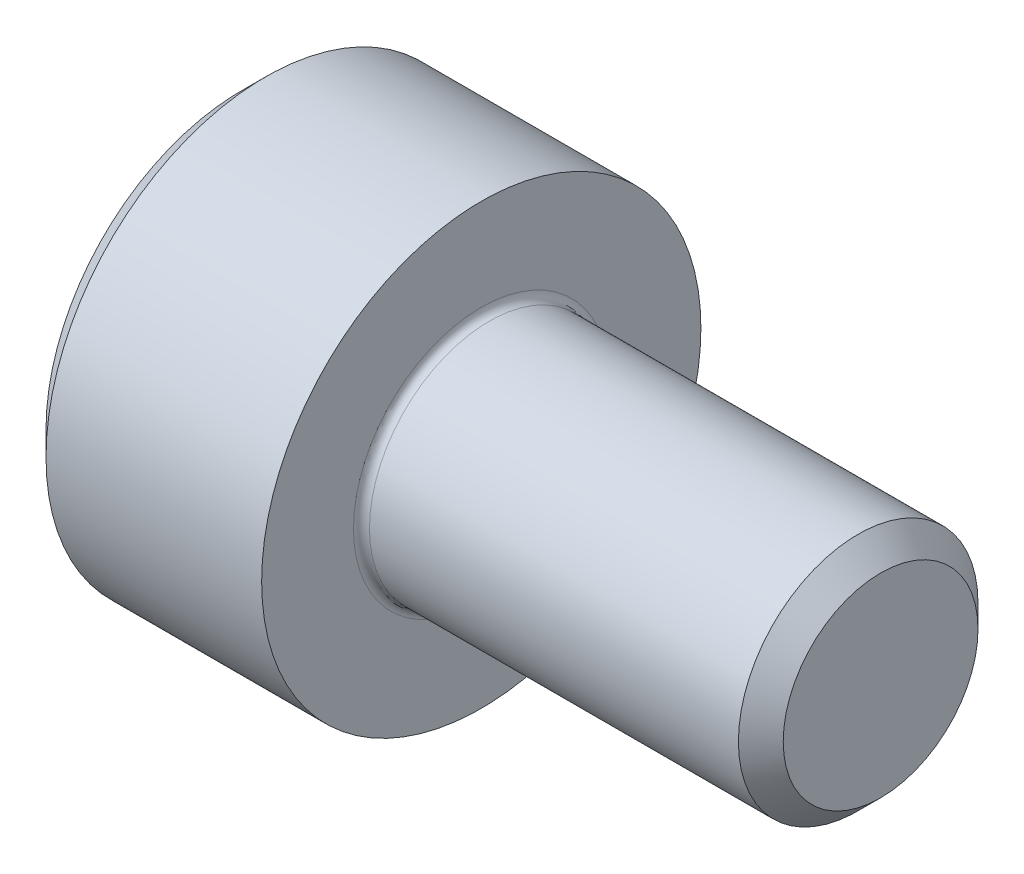
SolidWorks part; units mm, degrees
revolve "Base-Revolve" add sketch "BodySke"
sketch "BodySke" plane through (0, 0, 0) normal (0, 0, 1) x (1, 0, 0)
  line L0 (0, 0) -> (0, 2.45)
  line L1 (0.3, 2.75) -> (3, 2.75)
  line L2 (3, 2.75) -> (3, 1.5)
  line L3 (3, 1.5) -> (7.7195, 1.5)
  line L4 (8, 1.2195) -> (8, 0)
  line L5 (8, 0) -> (0, 0)
  line L6 (-31.75, 0) -> (127, 0) construction
  line L7 (0, 2.45) -> (0.3, 2.75)
  line L8 (8, 1.2195) -> (7.7195, 1.5)
  line L9 (0, -2.45) -> (0.3, -2.75) construction
  line L10 (8, -1.2195) -> (7.7195, -1.5) construction
  line L11 (3.5, 9.525) -> (3.5, 3.175) construction
  line L12 (-2, 9.525) -> (-2, 3.175) construction
  line L13 (-42, 9.525) -> (-42, 3.175) construction
  dimension "Diameter" = 3
  dimension "Head_ht" = 3
  dimension "Length" = 5
  dimension "Body_ch_ang" = 45
  dimension "Head_dia" = 5.5
  dimension "Head_ch_ang" = 45
  dimension "Minor_dia" = 2.439
  dimension "Advance" = 0.5
  dimension "Thread_nom" = 10
  dimension "Thread_length" = 50
  dimension "Head_ch_ht" = 0.3
cosmetic thread "ThreadCosmetic" [suppressed]
fillet "Fillet1" radius 0.1 1 edges at (3, 0, 1.5)
ref_plane "Plane1" through (0, 0, 0) normal (0, 0, 1) x (1, 0, 0)
ref_plane "Plane2" through (0, 0, 0) normal (0, 1, 0) x (1, 0, 0)
ref_plane "Plane3" through (0, 0, 0) normal (1, 0, 0) x (0, 0, -1)
sketch "Sketch2" plane through (0, 0, 0) normal (0, 0, 1) x (1, 0, 0)
  line L0 (0, 1.28) -> (1.3, 1.28)
  line L1 (1.3, 1.28) -> (2.039, 0)
  line L2 (-31.75, 0) -> (127, 0) construction
  line L3 (2.039, 0) -> (0, 0)
  line L4 (0, 0) -> (0, 1.28)
  line L5 (0, 2.45) -> (0, -2.45) construction
  line L6 (0, 0) -> (47.625, 0) construction
  line L7 (3, -2.75) -> (3, 2.75) construction
  dimension "D1" = 1.28
  dimension "D2" = 60
revolve "Hex-PreBroach" cut sketch "Sketch2" angle 360 about L6
sketch "Sketch3" plane through (0, 0, 0) normal (-1, 0, 0) x (0, 0.5, 0.866)
  line L0 (0.739, 1.28) -> (-0.739, 1.28)
  line L1 (-0.739, 1.28) -> (-1.478, 0)
  line L2 (0.739, 1.28) -> (1.478, 0)
  line L3 (0.739, -1.28) -> (1.478, 0)
  line L4 (0.739, -1.28) -> (-0.739, -1.28)
  line L5 (-0.739, -1.28) -> (-1.478, 0)
  dimension "D1" = 1.28
  dimension "D2" = 1.28
  dimension "Hex_size" = 2.56
extrude "Hex" cut sketch "Sketch3" against normal blind 1.3
sketch "Sketch4" plane through (0, 0, 0) normal (-1, 0, 0) x (0, 0, 1)
  line L0 (0, 0) -> (1.4605, 0)
  line L1 (0, 0) -> (6.1484, 3.5498) construction
  line L2 (0, 0) -> (0.7302, 1.2648)
  line L3 (1.2009, 0.3267) -> (1.3933, 0.4378)
  line L4 (0.8834, 0.8767) -> (1.0758, 0.9877)
  arc A0 (1.2009, 0.3267) -> (0.8834, 0.8767) centre (0, 0) ccw
  arc A1 (1.4605, 0) -> (1.3933, 0.4378) centre (0, 0) ccw
  arc A2 (0.7302, 1.2648) -> (1.0758, 0.9877) centre (0, 0) cw
  dimension "D1" = 30
  dimension "D2" = 60
  dimension "Spline_p_dim" = 0.635
  dimension "D3" = 0.3175
extrude "Spline" [suppressed] cut sketch "Sketch4" against normal blind 1.3
pattern_circular "CirPattern1" [suppressed] count 6 every 60
sketch "Sketch5" plane through (0, 0, 0) normal (0, 0, 1) x (1, 0, 0)
  line L0 (-31.75, 0) -> (127, 0) construction
  line L2 (0, 2.45) -> (0, -2.45) construction
  circle A0 centre (1.2, 0) radius 0.475
  dimension "Drilled_hole_dia" = 0.95
  dimension "Drilled_hole_loc" = 1.2
extrude "Hole" [suppressed] cut sketch "Sketch5" against normal through all and the other way through all
pattern_circular "Drilled-4" [suppressed] count 2 every 60
pattern_circular "Drilled-6" [suppressed] count 3 every 60
sketch "ThdSchSke" plane through (0, 0, 0) normal (0, 0, 1) x (1, 0, 0)
  line L0 (3.5, -1.2195) -> (3.3036, -1.5)
  line L1 (3.5, -1.2195) -> (3.6964, -1.5)
  line L2 (3.6964, -1.5) -> (3.6964, -1.875)
  line L3 (-3.175, 0) -> (5.1513, 0) construction
  line L5 (3.6964, -1.875) -> (3.3036, -1.875)
  line L6 (3.3036, -1.875) -> (3.3036, -1.5)
  line L7 (0, 2.45) -> (0, -2.45) construction
  dimension "Thread_minor" = 2.439
  dimension "Diameter" = 3
  dimension "Start" = 3.5
revolve "ThreadSchematic" [suppressed] cut sketch "ThdSchSke" angle 360 about L3
pattern_linear "ThdSchPat" [suppressed]
equation "\"D2@Sketch3\" = \"Hex_size@Sketch3\" / 2"
equation "\"D1@Sketch3\" = \"Hex_size@Sketch3\" / 2"
equation "\"D1@Sketch2\" = \"Hex_size@Sketch3\" / 2"
equation "\"D3@Sketch4\" = \"Spline_p_dim@Sketch4\" / 2"
equation "\"Thread_minor@ThreadCosmetic\"  =  \"Minor_dia@BodySke\""
equation "\"D2@CirPattern1\" = 360 / \"Num_teeth@CirPattern1\""
equation "\"Wall_thickness@Sketch2\" = \"Head_ht@BodySke\" - \"Key_eng@Hex\""
equation "\"Thread_length@ThreadCosmetic\" = ((sgn( (\"Length@BodySke\" - \"Advance@BodySke\" ) - \"Thread_nom@BodySke\" )-1)*( (\"Length@BodySke\" - \"Advance@BodySke\" ) - \"Thread_nom@BodySke\" ))/-2+ \"Thread_nom@BodySke\""
equation "\"Thread_minor@ThdSchSke\" = \"Minor_dia@BodySke\""
equation "\"Diameter@ThdSchSke\" = \"Diameter@BodySke\""
equation "\"Overcut@ThdSchSke\" = \"Diameter@BodySke\" * 1.25"
equation "\"Start@ThdSchSke\" = \"Head_ht@BodySke\" + \"Length@BodySke\" - \"Thread_length@ThreadCosmetic\"  '---Non-countersunk---"
equation "\"Num_threads@ThdSchPat\" = int( \"Thread_length@ThreadCosmetic\" / \"Advance@BodySke\" + 0.999 )  + 1"
equation "\"Advance@ThdSchPat\" = \"Thread_length@ThreadCosmetic\" /  (\"Num_threads@ThdSchPat\" - 1) 'relax it"
equation "\"Num_threads@ThdSchPat\" = \"Num_threads@ThdSchPat\" - sgn( \"Num_threads@ThdSchPat\" - 1) '---chamfered tips only---"
